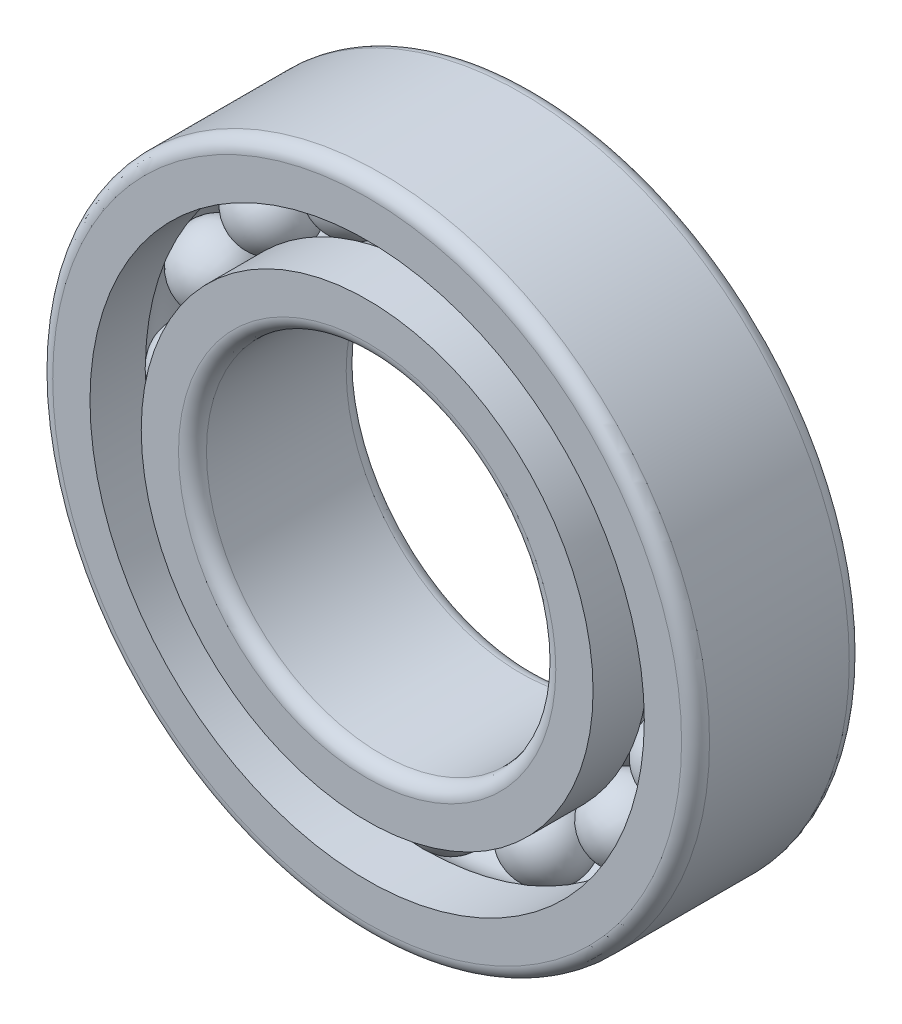
SolidWorks part; units mm, degrees
ref_plane "Front Plane" through (0, 0, 0) normal (0, 0, 1) x (1, 0, 0)
ref_plane "Top Plane" through (0, 0, 0) normal (0, 1, 0) x (1, 0, 0)
ref_plane "Right Plane" through (0, 0, 0) normal (1, 0, 0) x (0, 0, -1)
other "Configuration Table"
sketch "BaseSke" plane through (0, 0, 0) normal (1, 0, 0) x (0, 0, -1)
  line L0 (-47.2296, 0) -> (24.6132, 0) construction
  line L1 (-47.2296, 18) -> (24.6132, 18) construction
  line L2 (0, 129.5214) -> (0, -86.3012) construction
  line L3 (0, 20.75) -> (0, 15.25)
  line L4 (-6, 23.5) -> (6, 23.5) construction
  line L5 (-6, 12.5) -> (6, 12.5) construction
  arc A0 (0, 20.75) -> (0, 15.25) centre (0, 18) ccw
  dimension "Ball_diameter" = 5.5
  dimension "Bearing_Thickness" = 12
  dimension "Bearing_Outside_Diameter" = 47
  dimension "Bearing_Inside_Diameter" = 25
  dimension "D1" = 18
revolve "Ball" add sketch "BaseSke" angle 360 about L3
sketch "OuterRaceSke" plane through (0, 0, 0) normal (1, 0, 0) x (0, 0, -1)
  line L0 (0, 0) -> (0, 87.5396) construction
  line L1 (-6, 23.5) -> (6, 23.5)
  line L2 (-6, 23.5) -> (-6, 19.8333)
  line L3 (-6, 19.8333) -> (-2.0363, 19.8333)
  line L4 (6, 23.5) -> (6, 19.8333)
  line L5 (-50.3916, 0) -> (55.2197, 0) construction
  line L6 (-47.2296, 18) -> (24.6132, 18) construction
  line L7 (2.0363, 19.8333) -> (6, 19.8333)
  arc A0 (2.0363, 19.8333) -> (-2.0363, 19.8333) centre (0, 18) ccw
  dimension "D4" = 5.48
  dimension "D2" = 39.6667
revolve "OuterRace" add sketch "OuterRaceSke" angle 360 about L5
sketch "InnerRaceSke" plane through (0, 0, 0) normal (1, 0, 0) x (0, 0, -1)
  line L0 (-70.8626, 0) -> (113.5527, 0) construction
  line L1 (0, 58.441) -> (0, -70.8113) construction
  line L2 (-6, 12.5) -> (6, 12.5)
  line L3 (-6, 12.5) -> (-6, 16.1667)
  line L4 (-6, 16.1667) -> (-2.0363, 16.1667)
  line L5 (6, 12.5) -> (6, 16.1667)
  line L6 (0, 129.5214) -> (0, -86.3012) construction
  line L7 (2.0363, 16.1667) -> (6, 16.1667)
  arc A0 (-2.0363, 16.1667) -> (2.0363, 16.1667) centre (0, 18) ccw
  arc A1 (0, 20.75) -> (0, 15.25) centre (0, 18) ccw construction
  dimension "D2" = 5.48
  dimension "D1" = 32.3333
revolve "InnerRace" add sketch "InnerRaceSke" angle 360 about L0
fillet "Fillet1" radius 1 4 edges at (12.5, 0, -6) (12.5, 0, 6) (23.5, 0, -6) (23.5, 0, 6)
sketch "ShieldedSke" plane through (0, 0, 0) normal (1, 0, 0) x (0, 0, -1)
  line L1 (-5.5, 19.8333) -> (-4, 19.8333)
  line L2 (-6, 19.3333) -> (-6, 16.6667)
  line L3 (-5.5, 16.1667) -> (-4, 16.1667)
  line L4 (-4, 19.8333) -> (-4, 16.1667)
  arc A0 (-5.5, 19.8333) -> (-6, 19.3333) centre (-5.5, 19.3333) ccw
  arc A1 (-6, 16.6667) -> (-5.5, 16.1667) centre (-5.5, 16.6667) ccw
  point P12 (-6, 19.8333)
  point P13 (-6, 16.1667)
  dimension "D1" = 0.5
  dimension "D2" = 4
revolve "Shielded" [suppressed] add sketch "ShieldedSke" angle 360 about L0
mirror "DoubleShielded" [suppressed] about plane through (0, 0, 0) normal (0, 0, 1)
sketch "SealedSke" plane through (0, 0, 0) normal (1, 0, 0) x (0, 0, -1)
  line L0 (-34.5153, 0) -> (39.09, 0) construction
  line L1 (-24.8, 16.1667) -> (-4.8, 16.1667)
  line L2 (-24.8, 16.1667) -> (-24.8, 19.8333)
  line L3 (-24.8, 19.8333) -> (-4.8, 19.8333)
  line L4 (-4.8, 16.1667) -> (-4.8, 19.8333)
  dimension "D1" = 20
  dimension "D2" = 4.8
revolve "Sealed" [suppressed] cut sketch "SealedSke" angle 360 about L0
mirror "DoubleSealed" [suppressed] about plane through (0, 0, 0) normal (0, 0, 1)
pattern_circular "CirPatternBall" count 16 over 360 about axis through (0, 0, 0) along (0, 0, 1) of "Ball"
sketch "CutGrooveSke" plane through (0, 0, 0) normal (1, 0, 0) x (0, 0, -1)
  line L0 (-51.8407, 0) -> (83.8302, 0) construction
  line L1 (3.6, -43.03) -> (3, -43.03)
  line L2 (3.6, -43.03) -> (3.6, -23.03)
  line L3 (3.6, -23.03) -> (3, -23.03)
  line L4 (3, -43.03) -> (3, -23.03)
  dimension "D1" = 23.03
  dimension "D2" = 3
  dimension "D3" = 0.6
  dimension "D4" = 20
revolve "CutGroove" [suppressed] cut sketch "CutGrooveSke" angle 360 about L0
sketch "TaperSke" plane through (0, 0, 0) normal (1, 0, 0) x (0, 0, -1)
  line L0 (-6, 12.5) -> (6, 12.5)
  line L1 (6, 12.5) -> (6, 13.5)
  line L2 (6, 13.5) -> (-6, 12.5)
  line L7 (-41.2502, 0) -> (40.8606, 0) construction
  dimension "Taper" = 1
revolve "Taper" [suppressed] cut sketch "TaperSke" angle 360 about L7
fillet "Fillet2" [suppressed] radius 1
sketch "SimplifiedSke" plane through (0, 0, 0) normal (1, 0, 0) x (0, 0, -1)
  line L0 (37.5911, 0) -> (-37.5911, 0) construction
  circle A0 centre (0, 18) radius 2.75
  arc A1 (0, 20.75) -> (0, 15.25) centre (0, 18) ccw construction
revolve "Simplified" [suppressed] add sketch "SimplifiedSke" angle 360 about L0
equation "\"D1@BaseSke\" =  (\"Bearing_Outside_Diameter@BaseSke\"  +  \"Bearing_Inside_Diameter@BaseSke\"  )  / 4"
equation "\"Ball_diameter@BaseSke\" =  ( \"Bearing_Outside_Diameter@BaseSke\" - \"Bearing_Inside_Diameter@BaseSke\" ) / 4 "
equation "\"D2@OuterRaceSke\" = \"Bearing_Outside_Diameter@BaseSke\" -  ( \"Bearing_Outside_Diameter@BaseSke\" - \"Bearing_Inside_Diameter@BaseSke\" )  / 3"
equation "\"D4@OuterRaceSke\" = (  \"Bearing_Outside_Diameter@BaseSke\" - \"Bearing_Inside_Diameter@BaseSke\" ) / 4 -0.02"
equation "\"D1@InnerRaceSke\" = \"Bearing_Inside_Diameter@BaseSke\" +  ( \"Bearing_Outside_Diameter@BaseSke\" - \"Bearing_Inside_Diameter@BaseSke\" )  / 3"
equation "\"D2@InnerRaceSke\" = \"D4@OuterRaceSke\""
equation "\"D1@ShieldedSke\" = \"Fillet_radius@Fillet1\"/2"
equation "\"D2@ShieldedSke\" = \"Bearing_Thickness@BaseSke\"/3"
equation "\"D2@SealedSke\" = \"Bearing_Thickness@BaseSke\"/2.5"
equation "\"D1@CirPatternBall\" = int( \"D1@BaseSke\"* pi  * 2 / \"Ball_diameter@BaseSke\"/1.2 ) -1"
equation "\"D1@CutGrooveSke\" = \"Bearing_Outside_Diameter@BaseSke\" * 0.49"
equation "\"D2@CutGrooveSke\" = \"Bearing_Thickness@BaseSke\" *0.25"
equation "\"D3@CutGrooveSke\" = \"Bearing_Thickness@BaseSke\"/20"
equation "\"Taper@TaperSke\" = \"Bearing_Thickness@BaseSke\"/12"
equation "\"D1@Fillet2\" = \"Fillet_radius@Fillet1\""
